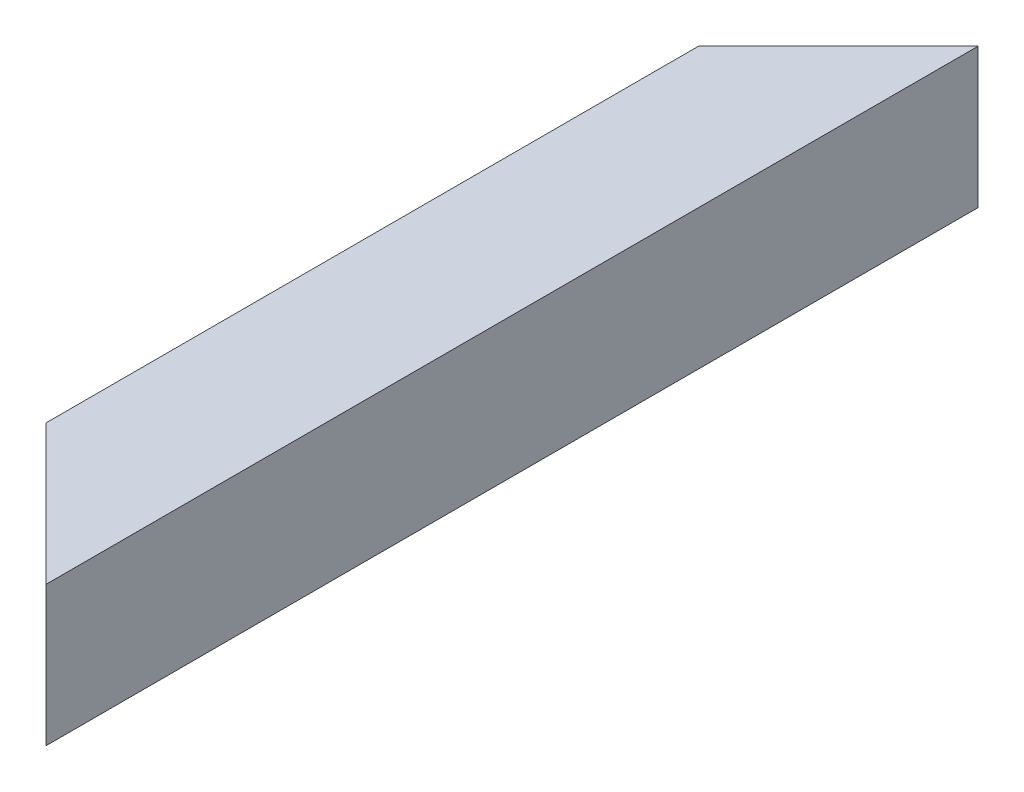
SolidWorks part; units mm, degrees
material "1.0037 (S235JR)"
ref_plane "Front Plane" through (0, 0, 0) normal (0, 0, 1) x (1, 0, 0)
ref_plane "Top Plane" through (0, 0, 0) normal (0, 1, 0) x (1, 0, 0)
ref_plane "Right Plane" through (0, 0, 0) normal (1, 0, 0) x (0, 0, -1)
curve "Curve1"
  spline degree 1 poles (0, 0, 0) (0, 0, 400) knots 0 0 1 1
sketch "Sketch1" plane through (0, 0, 0) normal (0, 0, 1) x (1, 0, 0)
  line L0 (0, 35.3535) -> (0, -33.8384) construction
  line L1 (-30, 30) -> (30, 30)
  line L2 (-30, 30) -> (-30, -30)
  line L3 (-30, -30) -> (30, -30)
  line L4 (30, 30) -> (30, -30)
  line L5 (-26, 26) -> (26, 26)
  line L6 (-26, 26) -> (-26, -26)
  line L7 (-26, -26) -> (26, -26)
  line L8 (26, 26) -> (26, -26)
  line L9 (-39.3939, 0) -> (41.5152, 0) construction
  dimension "D1" = 60
  dimension "D2" = 52
sweep "Sweep1" add profiles "Sketch1" path "Curve1"
sketch "Sketch2" plane through (0, 30, 0) normal (0, 1, 0) x (1, 0, 0)
  line L0 (30, 0) -> (-30, -60)
  line L1 (-30, 0) -> (-30, -400) construction
  line L2 (-30, -60) -> (-30, 0)
  line L3 (-30, 0) -> (30, 0)
  line L4 (30, -400) -> (-30, -340)
  line L5 (-30, -340) -> (-30, -400)
  line L6 (-30, -400) -> (30, -400)
  dimension "D1" = 45
  dimension "D2" = 45
extrude "Cut-Extrude1" cut sketch "Sketch2" against normal through all
